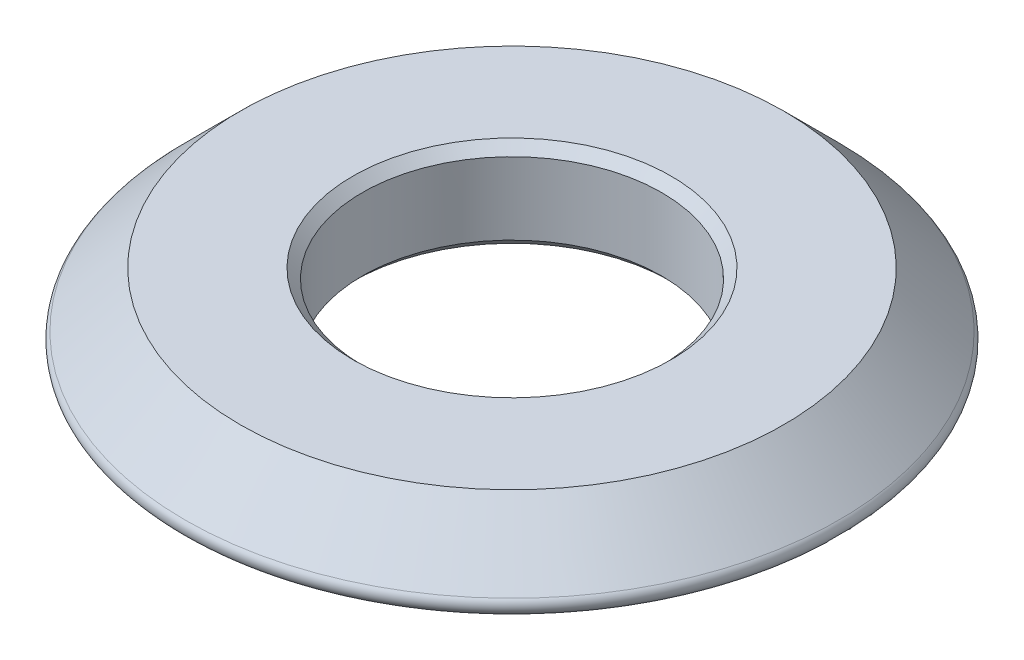
SolidWorks part; units mm, degrees
material "Markforged"
ref_plane "Front Plane" through (0, 0, 0) normal (0, 0, 1) x (1, 0, 0)
ref_plane "Top Plane" through (0, 0, 0) normal (0, 1, 0) x (1, 0, 0)
ref_plane "Right Plane" through (0, 0, 0) normal (1, 0, 0) x (0, 0, -1)
other "Bounding Box"
ref_plane "Default Plane" through (-8.9266, -12.7485, 0) normal (-0.1736, 0.9848, 0) x (0.9848, 0.1736, 0)
sketch "Sketch1" plane through (0, 0, 0) normal (1, 0, 0) x (0, 0, -1)
  line L0 (0, 0) -> (0, 8.0505) construction
  line L2 (4, 1.905) -> (7.2644, 1.905)
  line L3 (7.2644, 1.905) -> (9.1694, 0)
  line L4 (9.1694, 0) -> (4.943, 0)
  line L5 (4.943, 0) -> (4.635, -0.5334)
  line L6 (4.635, -0.5334) -> (4, -0.5334)
  line L8 (4, -0.5334) -> (4, 1.905)
  dimension "D1" = 7.2644
  dimension "D2" = 45
  dimension "D3" = 1.905
  dimension "D4" = 2.4384
  dimension "D5" = 0.635
  dimension "D6" = 8
  dimension "D7" = 30
revolve "Revolve1" add sketch "Sketch1" angle 360 about L0
sketch "Sketch2" plane through (0, 0, 0) normal (0, -1, 0) x (1, 0, 0)
  line L0 (-7.5544, 5.197) -> (7.5544, 5.197) construction
  circle A0 centre (0, 0) radius 9.1694 construction
  circle A1 centre (0, 0) radius 4.943 construction
  text T0 "<b>Out</b>\r\n" font "Comic Sans MS" height 2.54
  point P6 (0, 4.943)
  dimension "D1" = 0.254
extrude "Cut-Extrude1" cut sketch "Sketch2" against normal blind 0.254
fillet "Fillet1" radius 0.254 1 edges at (0, 0, -9.1694)
chamfer "Chamfer1" distance 0.254 angle 45 2 edges at (0, 1.905, -4) (0, -0.5334, -4)
